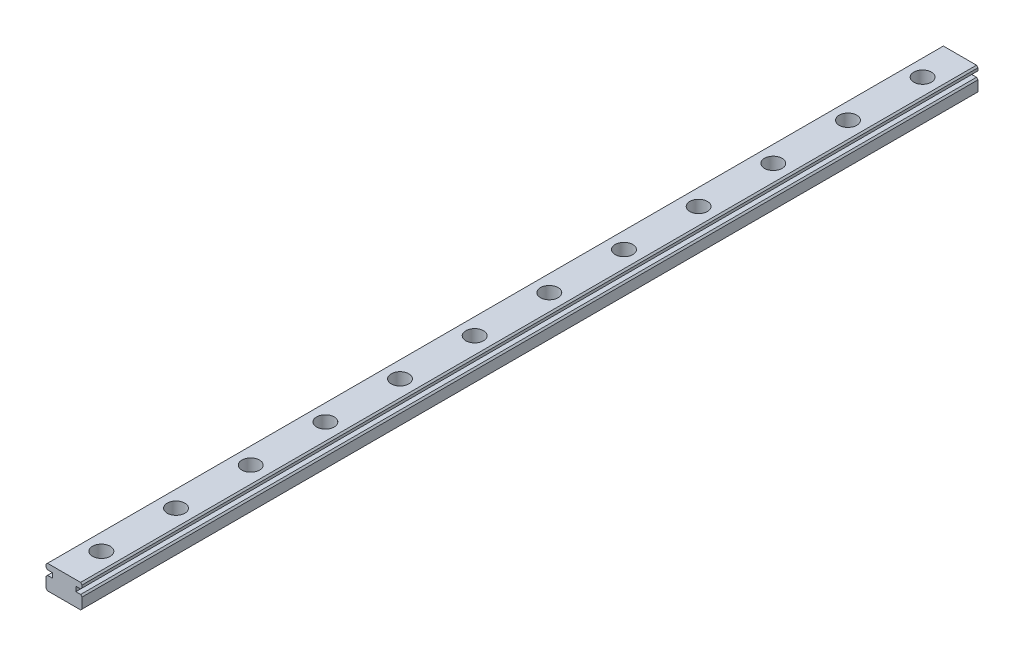
SolidWorks part; units mm, degrees
ref_plane "Front Plane" through (0, 0, 0) normal (0, 0, 1) x (1, 0, 0)
ref_plane "Top Plane" through (0, 0, 0) normal (0, 1, 0) x (1, 0, 0)
ref_plane "Right Plane" through (0, 0, 0) normal (1, 0, 0) x (0, 0, -1)
sketch "Sketch1" plane through (0, 0, 0) normal (0, 0, 1) x (1, 0, 0)
  line L0 (6.05, 2.1) -> (3.95, 2.1)
  line L1 (-6.05, 4) -> (6.05, 4)
  line L2 (-6.05, 4) -> (-6.05, 2.1)
  line L3 (-6.05, -4) -> (6.05, -4)
  line L4 (6.05, 4) -> (6.05, 2.1)
  line L5 (-6.05, 4) -> (6.05, -4) construction
  line L6 (-6.05, -4) -> (6.05, 4) construction
  line L7 (3.95, 2.1) -> (3.95, 0.5)
  line L8 (3.95, 0.5) -> (6.05, 0.5)
  line L9 (0, 0) -> (0, 2.5782)
  line L10 (-3.95, 0.5) -> (-6.05, 0.5)
  line L11 (-3.95, 2.1) -> (-3.95, 0.5)
  line L12 (-6.05, 2.1) -> (-3.95, 2.1)
  line L13 (-6.05, 0.5) -> (-6.05, -4)
  line L14 (6.05, 0.5) -> (6.05, -4)
  point P0 (0, 0)
  dimension "D1" = 12.1
  dimension "D2" = 8
  dimension "D3" = 1.9
  dimension "D4" = 1.6
  dimension "D5" = 2.1
extrude "Boss-Extrude1" add sketch "Sketch1" along normal blind 300
chamfer "Chamfer1" distance 0.5 angle 45 8 edges at (6.05, -4, 150) (-6.05, -4, 150) (-6.05, 0.5, 150) (-6.05, 2.1, 150) (-6.05, 4, 150) (6.05, 4, 150) (6.05, 2.1, 150) (6.05, 0.5, 150)
sketch "Sketch2" plane through (0, 4, 0) normal (0, 1, 0) x (1, 0, 0)
  line L0 (5.55, -150) -> (-5.55, -150)
  line L1 (5.55, -300) -> (5.55, 0) construction
  line L2 (-5.55, 0) -> (-5.55, -300) construction
  line L3 (-5.55, 0) -> (5.55, 0) construction
  circle A0 centre (0, -137.5) radius 2.95
  circle A1 centre (0, -162.5) radius 2.95
  dimension "D4" = 5.9
  dimension "D5" = 5.9
  dimension "D1" = 150
  dimension "D2" = 12.5
  dimension "D3" = 12.5
extrude "Cut-Extrude1" cut sketch "Sketch2" against normal blind 5.6 contours A1 | A0
pattern_linear "LPattern1" count 6 spacing 25 along (0, 0, 1) of "Cut-Extrude1"
pattern_linear "LPattern2" count 7 spacing 25 along (0, 0, -1) of "Cut-Extrude1"
sketch "Sketch3" plane through (0, 4, 0) normal (0, 1, 0) x (1, 0, 0)
  circle A0 centre (0, -162.5) radius 1.6
  circle A1 centre (0, -137.5) radius 1.6
  dimension "D1" = 3.2
  dimension "D2" = 3.2
extrude "Cut-Extrude2" cut sketch "Sketch3" against normal through all
pattern_linear "LPattern3" count 7 spacing 25 along (0, 0, -1) count 6 spacing 25 along (0, 0, 1) of "Cut-Extrude2"
equation "\"length\"= 300mm"
equation "\"D1@Sketch2\"=\"length\"/2"
equation "\"holeSpacing\"= 25mm"
equation "\"D2@Sketch2\"=\"holeSpacing\"/2"
equation "\"D3@Sketch2\"=\"holeSpacing\"/2"
equation "\"D3@LPattern1\"=\"holeSpacing\""
equation "\"D3@LPattern2\"=\"holeSpacing\""
equation "\"D3@LPattern3\"=\"holeSpacing\""
equation "\"D4@LPattern3\"=\"holeSpacing\""
equation "\"endDist\"= \"RD3@Annotations\""
equation "\"D1@Boss-Extrude1\"=\"length\""
